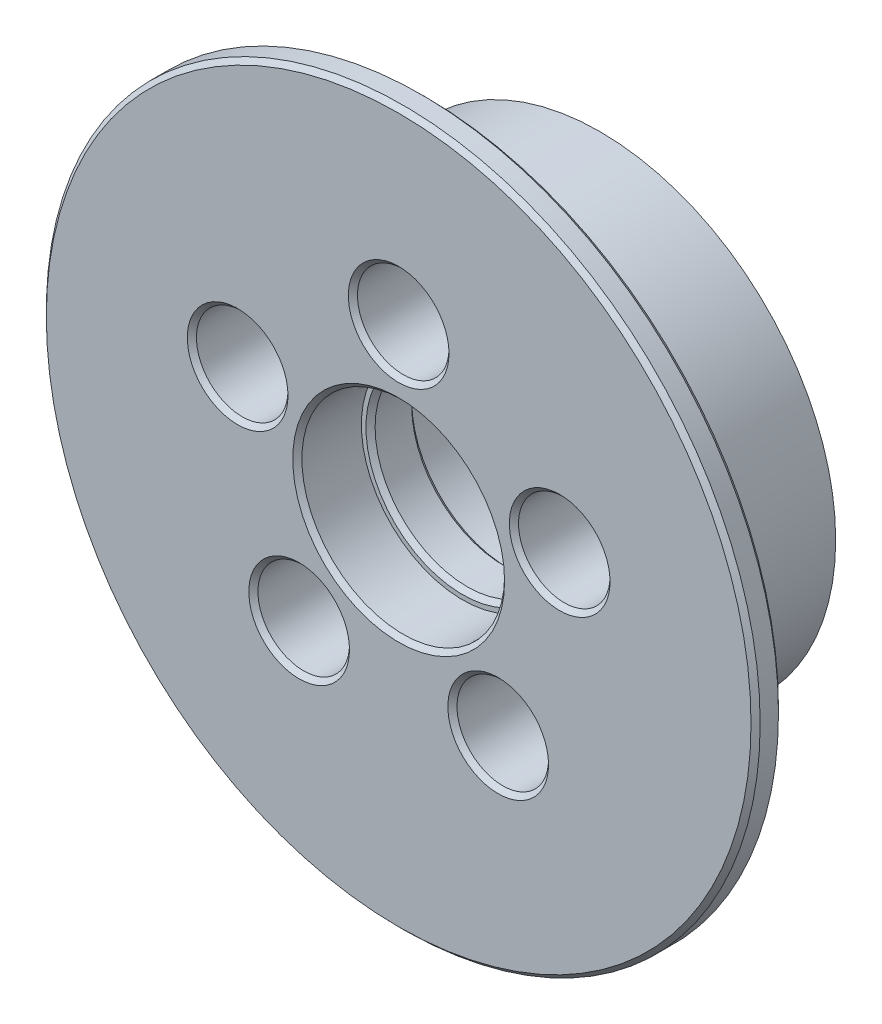
SolidWorks part; units mm, degrees
ref_plane "Front Plane" through (0, 0, 0) normal (0, 0, 1) x (1, 0, 0)
ref_plane "Top Plane" through (0, 0, 0) normal (0, 1, 0) x (1, 0, 0)
ref_plane "Right Plane" through (0, 0, 0) normal (1, 0, 0) x (0, 0, -1)
sketch "Sketch1" plane through (0, 0, 0) normal (0, 0, 1) x (1, 0, 0)
  circle A0 centre (0, 0) radius 25.75
  dimension "D1" = 51.5
extrude "Boss-Extrude1" add sketch "Sketch1" along normal blind 19
sketch "Sketch2" plane through (0, 0, 19) normal (0, 0, 1) x (1, 0, 0)
  circle A0 centre (0, 0) radius 39
  dimension "D1" = 78
extrude "Boss-Extrude2" add sketch "Sketch2" along normal blind 3
sketch "Sketch3" plane through (0, 0, 0) normal (0, 0, -1) x (-1, 0, 0)
  circle A0 centre (0, 0) radius 18.5 construction
  circle A1 centre (0, 18.5) radius 5
  circle A2 centre (17.5945, 5.7168) radius 5
  circle A3 centre (10.874, -14.9668) radius 5
  circle A4 centre (-10.874, -14.9668) radius 5
  circle A5 centre (-17.5945, 5.7168) radius 5
  point P16 (0, 0)
  dimension "D2" = 10
  dimension "D3" = 37
  dimension "D1" = 5
extrude "Cut-Extrude1" cut sketch "Sketch3" against normal through all
sketch "Sketch4" plane through (0, 0, 0) normal (0, 0, -1) x (-1, 0, 0)
  circle A0 centre (0, 0) radius 10.075
  dimension "D1" = 20.15
extrude "Cut-Extrude2" cut sketch "Sketch4" against normal through all
sketch "Sketch5" plane through (0, 0, 0) normal (0, 0, -1) x (-1, 0, 0)
  circle A0 centre (0, 0) radius 11.075
  circle A3 centre (0, 0) radius 10.075 construction
  dimension "D1" = 1
extrude "Cut-Extrude3" cut sketch "Sketch5" against normal blind 10
sketch "Sketch6" plane through (0, 0, 22) normal (0, 0, 1) x (1, 0, 0)
  circle A0 centre (0, 0) radius 11.075
  circle A3 centre (0, 0) radius 10.075 construction
  dimension "D1" = 1
extrude "Cut-Extrude4" cut sketch "Sketch6" against normal blind 7
chamfer "Chamfer1" distance 0.5 angle 45 11 edges at (11.075, 0, 22) (-15.874, -14.9668, 22) (5.874, -14.9668, 22) (12.5945, 5.7168, 22) (-5, 18.5, 22) (-22.5945, 5.7168, 22) (-11.075, 0, 0) (-10.075, 0, 10) (10.075, 0, 15) (39, 0, 22) (39, 0, 19)
fillet "Fillet1" radius 1 5 edges at (-5, 18.5, 0) (-22.5945, 5.7168, 0) (-15.874, -14.9668, 0) (5.874, -14.9668, 0) (12.5945, 5.7168, 0)
